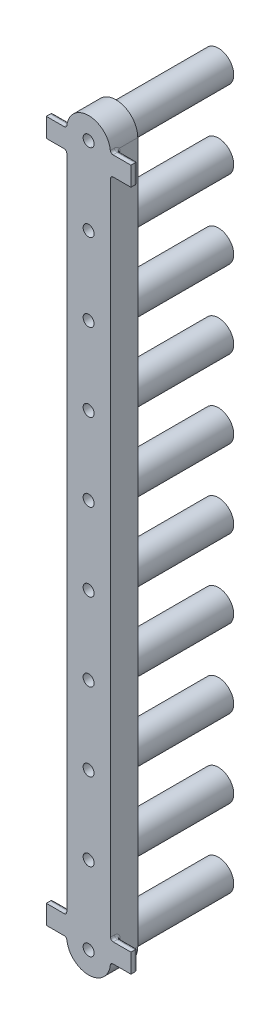
SolidWorks part; units mm, degrees
ref_plane "Ön Düzlem" through (0, 0, 0) normal (1, 0, 0) x (0, 1, 0)
ref_plane "Üst Düzlem" through (0, 0, 0) normal (0, 0, 1) x (0, 1, 0)
ref_plane "Sağ Düzlem" through (0, 0, 0) normal (0, 1, 0) x (-1, 0, 0)
sketch "Sketch1" plane through (0, 0, 0) normal (0, 0, 1) x (0, 1, 0)
  line L0 (0, 0) -> (102.6, 0) construction
  line L1 (0, 3.2) -> (102.6, 3.2)
  line L2 (0, -3.2) -> (102.6, -3.2)
  arc A0 (0, 3.2) -> (0, -3.2) centre (0, 0) ccw
  arc A1 (102.6, -3.2) -> (102.6, 3.2) centre (102.6, 0) ccw
  circle A2 centre (0, 0) radius 2.2 construction
  circle A3 centre (11.4, 0) radius 2.2 construction
  circle A4 centre (22.8, 0) radius 2.2 construction
  circle A5 centre (34.2, 0) radius 2.2 construction
  circle A6 centre (45.6, 0) radius 2.2 construction
  circle A7 centre (57, 0) radius 2.2 construction
  circle A8 centre (68.4, 0) radius 2.2 construction
  circle A9 centre (79.8, 0) radius 2.2 construction
  circle A10 centre (91.2, 0) radius 2.2 construction
  circle A11 centre (102.6, 0) radius 2.2 construction
  point P3 (51.3, 0)
  dimension "D2" = 10
  dimension "D1" = 3.2
extrude "Boss-Extrude1" add sketch "Sketch1" along normal blind 4
sketch "Sketch2" plane through (0, 0, 0) normal (0, 0, -1) x (1, 0, 0)
  circle A0 centre (0, 0) radius 2.25
  circle A1 centre (0, -11.4) radius 2.25
  circle A2 centre (0, -22.8) radius 2.25
  circle A3 centre (0, -34.2) radius 2.25
  circle A4 centre (0, -45.6) radius 2.25
  circle A5 centre (0, -57) radius 2.25
  circle A6 centre (0, -68.4) radius 2.25
  circle A7 centre (0, -79.8) radius 2.25
  circle A8 centre (0, -91.2) radius 2.25
  circle A9 centre (0, -102.6) radius 2.25
  dimension "D1" = 10
  dimension "D2" = 4.5
extrude "Boss-Extrude3" add sketch "Sketch2" along normal blind 15
fillet "Fillet1" radius 0.4 10 edges at (2.25, 79.8, 0) (2.25, 91.2, 0) (2.25, 102.6, 0) (2.25, 68.4, 0) (2.25, 57, 0) (2.25, 45.6, 0) (2.25, 34.2, 0) (2.25, 22.8, 0) (2.25, 11.4, 0) (2.25, 0, 0)
sketch "Sketch3" plane through (-3.2, 0, 0) normal (-1, 0, 0) x (0, -1, 0)
  line L0 (-2.8009, 4) -> (0, 4)
  line L1 (-102.6, 4) -> (-99.7991, 4)
  line L2 (-102.6, 4) -> (-102.6, 3)
  line L3 (-102.6, 3) -> (-99.7991, 3)
  line L4 (-99.7991, 4) -> (-99.7991, 3)
  line L5 (-2.8009, 4) -> (-2.8009, 3)
  line L6 (-2.8009, 3) -> (0, 3)
  line L7 (0, 4) -> (0, 3)
  dimension "D1" = 1
sketch "Sketch4" plane through (3.2, 0, 0) normal (1, 0, 0) x (0, 1, 0)
  line L1 (0, 4) -> (2.8009, 4)
  line L2 (0, 4) -> (0, 3)
  line L3 (0, 3) -> (2.8009, 3)
  line L4 (2.8009, 4) -> (2.8009, 3)
  line L5 (102.6, 4) -> (99.7991, 4)
  line L6 (102.6, 4) -> (102.6, 3)
  line L7 (102.6, 3) -> (99.7991, 3)
  line L8 (99.7991, 4) -> (99.7991, 3)
extrude "Boss-Extrude4" add sketch "Sketch4" along normal blind 3
extrude "Boss-Extrude5" add sketch "Sketch3" along normal blind 3
fillet "Fillet2" radius 0.4 12 edges at (-4.7, 2.8009, 3) (-6.2, 1.4005, 3) (-4.7, 0, 3) (4.7, 0, 3) (6.2, 1.4005, 3) (4.7, 2.8009, 3) (-4.7, 99.7991, 3) (-6.2, 101.1995, 3) (-4.7, 102.6, 3) (4.7, 99.7991, 3) (6.2, 101.1995, 3) (4.7, 102.6, 3)
fillet "Fillet3" radius 0.4 20 edges at (3.2, 0, 3.7) (3.2, 0.1172, 3.1172) (3.2, 2.8009, 3.7) (3.2, 2.6837, 3.1172) (-3.2, 2.8009, 3.7) (-3.2, 2.6837, 3.1172) (-3.2, 0, 3.7) (-3.2, 0.1172, 3.1172) (-3.2, 102.6, 3.7) (-3.2, 102.4828, 3.1172) (-3.2, 99.7991, 3.7) (-3.2, 99.9163, 3.1172) (3.2, 99.7991, 3.7) (3.2, 99.9163, 3.1172) (3.2, 102.6, 3.7) (3.2, 102.4828, 3.1172) (3.2, 1.4005, 3) (-3.2, 1.4005, 3) (-3.2, 101.1995, 3) (3.2, 101.1995, 3)
sketch "Sketch5" plane through (0, 0, -15) normal (0, 0, -1) x (1, 0, 0)
  circle A0 centre (0, 0) radius 0.8033
  circle A1 centre (0, -11.4) radius 0.8033
  circle A2 centre (0, -22.8) radius 0.8033
  circle A3 centre (0, -34.2) radius 0.8033
  circle A4 centre (0, -45.6) radius 0.8033
  circle A5 centre (0, -57) radius 0.8033
  circle A6 centre (0, -68.4) radius 0.8033
  circle A7 centre (0, -79.8) radius 0.8033
  circle A8 centre (0, -91.2) radius 0.8033
  circle A9 centre (0, -102.6) radius 0.8033
  dimension "D1" = 10
extrude "Cut-Extrude2" cut sketch "Sketch5" against normal through all
